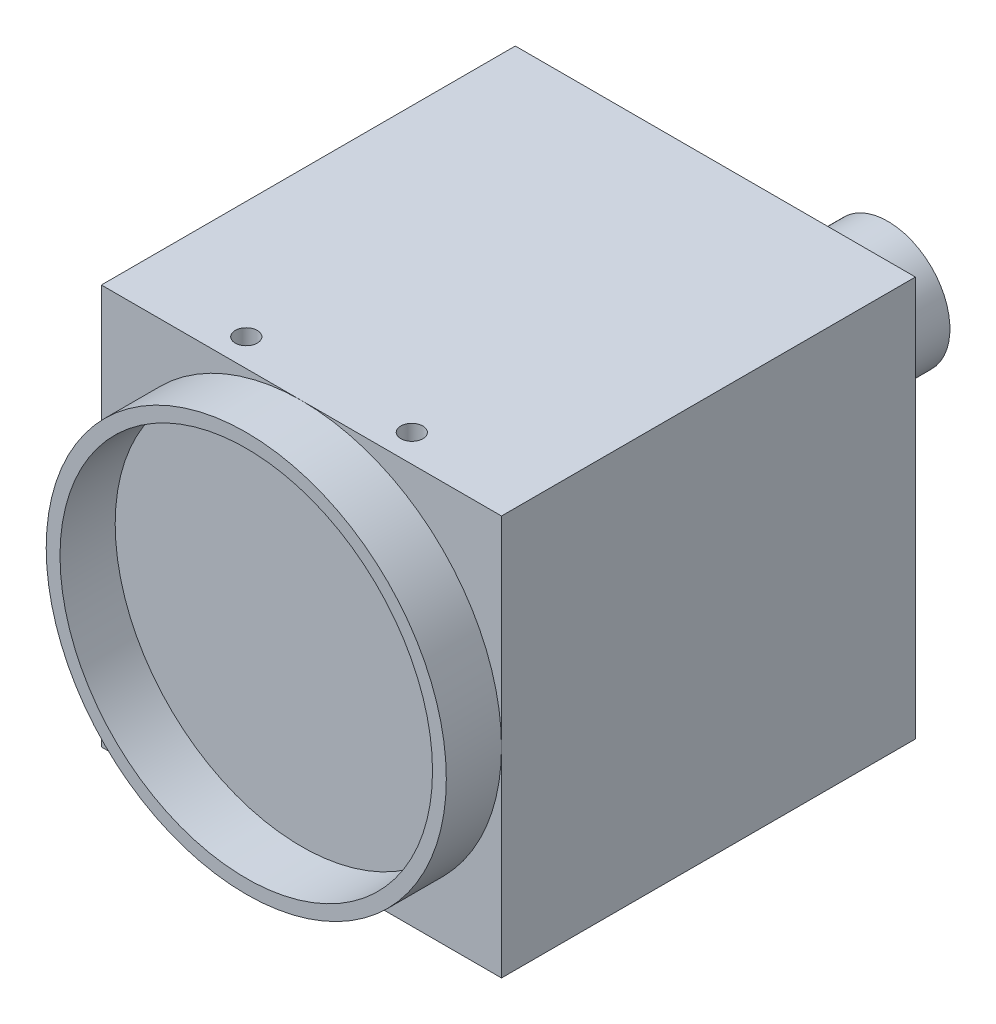
SolidWorks part; units mm, degrees
ref_plane "Front" through (0, 0, 0) normal (0, 0, 1) x (1, 0, 0)
ref_plane "Top" through (0, 0, 0) normal (0, 1, 0) x (1, 0, 0)
ref_plane "Right" through (0, 0, 0) normal (1, 0, 0) x (0, 0, -1)
sketch "Sketch1" plane through (0, 0, 0) normal (0, 0, 1) x (1, 0, 0)
  line L1 (-14.5, -14.5) -> (14.5, -14.5)
  line L2 (-14.5, -14.5) -> (-14.5, 14.5)
  line L3 (-14.5, 14.5) -> (14.5, 14.5)
  line L4 (14.5, -14.5) -> (14.5, 14.5)
  line L5 (-14.5, -14.5) -> (14.5, 14.5) construction
  line L6 (-14.5, 14.5) -> (14.5, -14.5) construction
  point P0 (0, 0)
  dimension "D1" = 29
  dimension "D2" = 29
extrude "Boss-Extrude1" add sketch "Sketch1" along normal blind 30
hole_wizard "M2x0.4 Tapped Hole1" positions "Sketch2" profile "Sketch3" tap size "M2x0.4" standard "ANSI Metric"
sketch "Sketch2" plane through (0, 14.5, 0) normal (0, 1, 0) x (1, 0, 0)
  line L0 (0, 4.7495) -> (0, -39.8018) construction
  line L2 (14.5, -30) -> (-14.5, -30) construction
  point P0 (-6, -28)
  point P14 (6, -28)
  dimension "D1" = 2
  dimension "D2" = 6
sketch "Sketch3" plane through (-6, 14.5, 28) normal (1, 0, 0) x (0, 0, 1)
  line L0 (0, 0) -> (0, 2.9807)
  line L1 (0, 2.9807) -> (0.8, 2.5)
  line L2 (0.8, 2.5) -> (0.8, 0)
  line L5 (0.8, 0) -> (0, 0)
  line L10 (0, 2.9807) -> (-0.8, 2.5) construction
  line L11 (0, -6.35) -> (0, 107.95) construction
  dimension "Tap Drill Dia." = 1.6
  dimension "Tap Drill Depth" = 2.5
  dimension "Drill Angle" = 118
cosmetic thread "Hole Thread1" parameters "D1"=2.5, "D2"=2
cosmetic thread "Hole Thread2" parameters "D1"=2.5, "D2"=2
hole_wizard "M3x0.5 Tapped Hole1" positions "Sketch4" profile "Sketch5" tap size "M3x0.5" standard "ANSI Metric"
sketch "Sketch4" plane through (0, -14.5, 0) normal (0, -1, 0) x (-1, 0, 0)
  line L0 (0, 8.998) -> (0, -34.5199) construction
  line L1 (14.5, -30) -> (-14.5, -30) construction
  point P0 (-10, -27)
  point P14 (10, -27)
  dimension "D1" = 3
  dimension "D2" = 10
sketch "Sketch5" plane through (10, -14.5, 27) normal (1, 0, 0) x (0, 0, -1)
  line L0 (0, 0) -> (0, 3.5511)
  line L1 (0, 3.5511) -> (1.25, 2.8)
  line L2 (1.25, 2.8) -> (1.25, 0)
  line L5 (1.25, 0) -> (0, 0)
  line L10 (0, 3.5511) -> (-1.25, 2.8) construction
  line L11 (0, -6.35) -> (0, 107.95) construction
  dimension "Tap Drill Dia." = 2.5
  dimension "Tap Drill Depth" = 2.8
  dimension "Drill Angle" = 118
cosmetic thread "Hole Thread3" parameters "D1"=2.8, "D2"=3
cosmetic thread "Hole Thread4" parameters "D1"=2.8, "D2"=3
hole_wizard "M3x0.5 Tapped Hole2" positions "Sketch6" profile "Sketch7" tap size "M3x0.5" standard "ANSI Metric"
sketch "Sketch6" plane through (0, -14.5, 0) normal (0, -1, 0) x (-1, 0, 0)
  line L4 (0, 1.4118) -> (0, -31.4118) construction
  point P0 (0, -3.3)
  dimension "D1" = 23.7
sketch "Sketch7" plane through (0, -14.5, 3.3) normal (1, 0, 0) x (0, 0, -1)
  line L0 (0, 0) -> (0, 3.2511)
  line L1 (0, 3.2511) -> (1.25, 2.5)
  line L2 (1.25, 2.5) -> (1.25, 0)
  line L5 (1.25, 0) -> (0, 0)
  line L10 (0, 3.2511) -> (-1.25, 2.5) construction
  line L11 (0, -6.35) -> (0, 107.95) construction
  dimension "Tap Drill Dia." = 2.5
  dimension "Tap Drill Depth" = 2.5
  dimension "Drill Angle" = 118
cosmetic thread "Hole Thread5" parameters "D1"=2.5, "D2"=3
hole_wizard "M2x0.4 Tapped Hole2" positions "Sketch8" profile "Sketch9" tap size "M2x0.4" standard "ANSI Metric"
sketch "Sketch8" plane through (0, -14.5, 0) normal (0, -1, 0) x (-1, 0, 0)
  line L0 (0, 1.293) -> (0, -32.0057) construction
  line L2 (14.5, -30) -> (-14.5, -30) construction
  point P0 (-6, -25.5)
  point P10 (6, -25.5)
  dimension "D1" = 6
  dimension "D2" = 4.5
sketch "Sketch9" plane through (6, -14.5, 25.5) normal (1, 0, 0) x (0, 0, -1)
  line L0 (0, 0) -> (0, 2.9807)
  line L1 (0, 2.9807) -> (0.8, 2.5)
  line L2 (0.8, 2.5) -> (0.8, 0)
  line L5 (0.8, 0) -> (0, 0)
  line L10 (0, 2.9807) -> (-0.8, 2.5) construction
  line L11 (0, -6.35) -> (0, 107.95) construction
  dimension "Tap Drill Dia." = 1.6
  dimension "Tap Drill Depth" = 2.5
  dimension "Drill Angle" = 118
cosmetic thread "Hole Thread6" parameters "D1"=2.5, "D2"=2
cosmetic thread "Hole Thread7" parameters "D1"=2.5, "D2"=2
hole_wizard "M2x0.4 Tapped Hole3" positions "Sketch10" profile "Sketch11" tap size "M2x0.4" standard "ANSI Metric"
sketch "Sketch10" plane through (0, -14.5, 0) normal (0, -1, 0) x (-1, 0, 0)
  line L0 (0, 1.5701) -> (0, -32.3224) construction
  point P0 (-6, -3.3)
  point P9 (6, -3.3)
  dimension "D1" = 6
  dimension "D2" = 23.7
sketch "Sketch11" plane through (6, -14.5, 3.3) normal (1, 0, 0) x (0, 0, -1)
  line L0 (0, 0) -> (0, 2.4807)
  line L1 (0, 2.4807) -> (0.8, 2)
  line L2 (0.8, 2) -> (0.8, 0)
  line L5 (0.8, 0) -> (0, 0)
  line L10 (0, 2.4807) -> (-0.8, 2) construction
  line L11 (0, -6.35) -> (0, 107.95) construction
  dimension "Tap Drill Dia." = 1.6
  dimension "Tap Drill Depth" = 2
  dimension "Drill Angle" = 118
cosmetic thread "Hole Thread8" parameters "D1"=2, "D2"=2
cosmetic thread "Hole Thread9" parameters "D1"=2, "D2"=2
sketch "Sketch12" plane through (0, 0, 0) normal (0, 0, -1) x (-1, 0, 0)
  line L1 (-5, -11) -> (5, -11)
  line L2 (-5, -11) -> (-5, -9)
  line L3 (-5, -9) -> (5, -9)
  line L4 (5, -11) -> (5, -9)
  line L5 (-5, -11) -> (5, -9) construction
  line L6 (-5, -9) -> (5, -11) construction
  circle A0 centre (6.5, -10.0003) radius 1.0003
  circle A1 centre (-6.5, -10) radius 1
  point P0 (0, -10)
  dimension "D1" = 1.5
  dimension "D2" = 2.0006
  dimension "D4" = 2
  dimension "D3" = 1.5
  dimension "D5" = 10
  dimension "D6" = 10
  dimension "D7" = 2
extrude "Cut-Extrude4" cut sketch "Sketch12" against normal blind 3
sketch "Sketch13" plane through (0, 0, 0) normal (0, 0, -1) x (-1, 0, 0)
  line L0 (-14.5, -14.5) -> (-14.5, 14.5) construction
  line L1 (-14.5, 14.5) -> (14.5, 14.5) construction
  circle A0 centre (-8.5, 8.5) radius 4.5
  dimension "D1" = 9
  dimension "D2" = 6
  dimension "D3" = 6
extrude "Boss-Extrude2" add sketch "Sketch13" along normal blind 4
sketch "Sketch14" plane through (0, 0, 30) normal (0, 0, 1) x (1, 0, 0)
  line L0 (14.5, 14.5) -> (-14.5, 14.5) construction
  circle A0 centre (0, 0) radius 14.5
  circle A1 centre (0, 0) radius 13.5
  dimension "D1" = 1
extrude "Boss-Extrude3" add sketch "Sketch14" along normal blind 4
